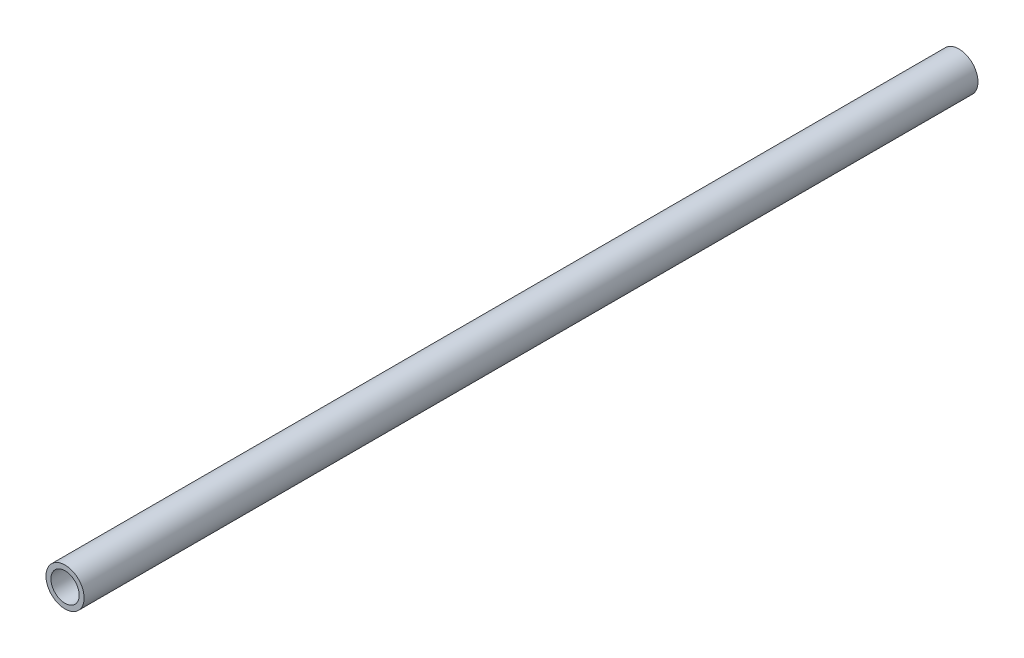
SolidWorks part; units mm, degrees
ref_plane "Front Plane" through (0, 0, 0) normal (0, 0, 1) x (1, 0, 0)
ref_plane "Top Plane" through (0, 0, 0) normal (0, 1, 0) x (1, 0, 0)
ref_plane "Right Plane" through (0, 0, 0) normal (1, 0, 0) x (0, 0, -1)
sketch "Sketch1" plane through (0, 0, 0) normal (0, 0, 1) x (1, 0, 0)
  circle A0 centre (0, 0) radius 10.668
  dimension "Pipe OD" = 21.336
extrude "Extrude-Thin1" add sketch "Sketch1" along normal mid plane 500 thin thin type one direction reverse wall 2.7686
